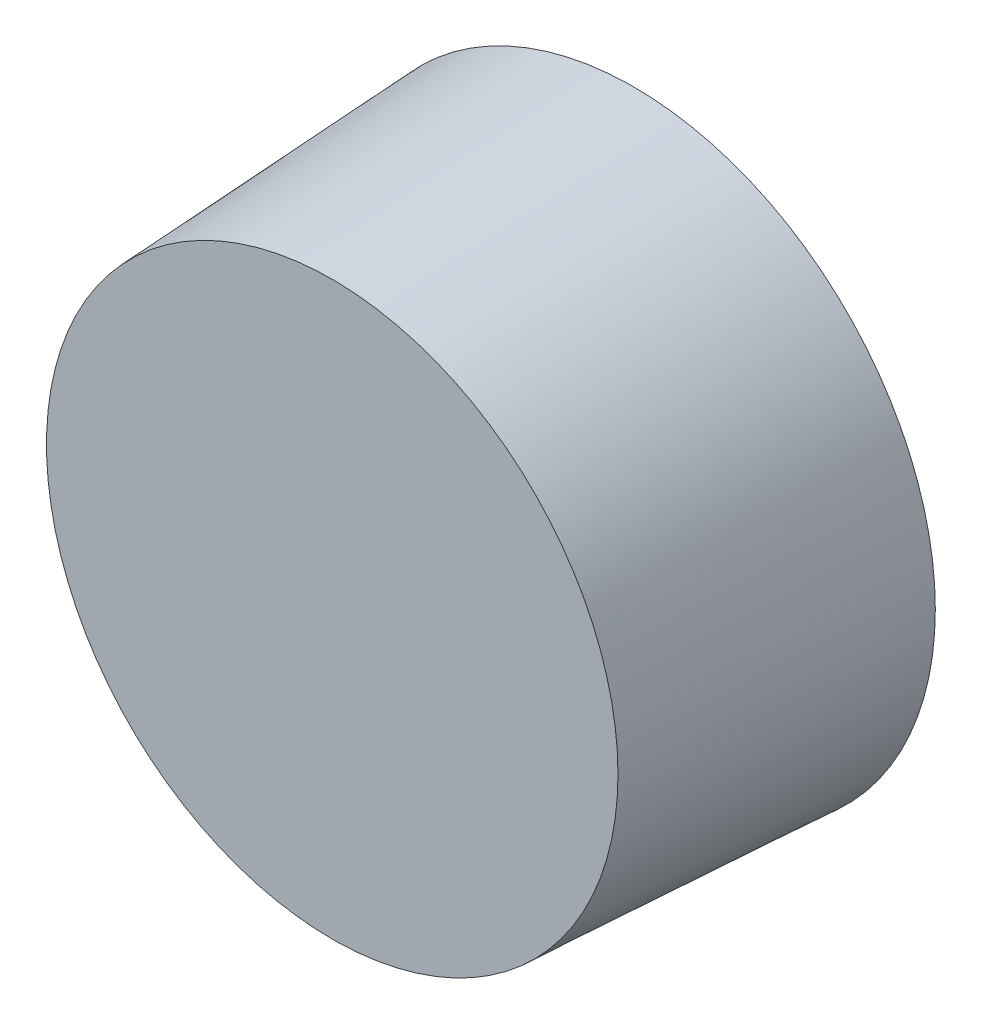
SolidWorks part; units mm, degrees
ref_plane "Płaszczyzna przednia" through (0, 0, 0) normal (0, 0, 1) x (1, 0, 0)
ref_plane "Płaszczyzna górna" through (0, 0, 0) normal (0, 1, 0) x (1, 0, 0)
ref_plane "Płaszczyzna prawa" through (0, 0, 0) normal (1, 0, 0) x (0, 0, -1)
sketch "Szkic1" plane through (0, 0, 0) normal (0, 0, 1) x (1, 0, 0)
  circle A0 centre (0, 0) radius 50
  dimension "D1" = 100
extrude "Dodanie-wyciągnięcie1" add sketch "Szkic1" along normal blind 50 draft 3
sketch "Szkic2" plane through (0, 0, 0) normal (0, 0, -1) x (-1, 0, 0)
  circle A2 centre (0, 0) radius 40
  circle A3 centre (0, 0) radius 40
  dimension "D1" = 10
extrude "Wytnij-wyciągnięcie1" cut sketch "Szkic2" against normal blind 20 draft 1
